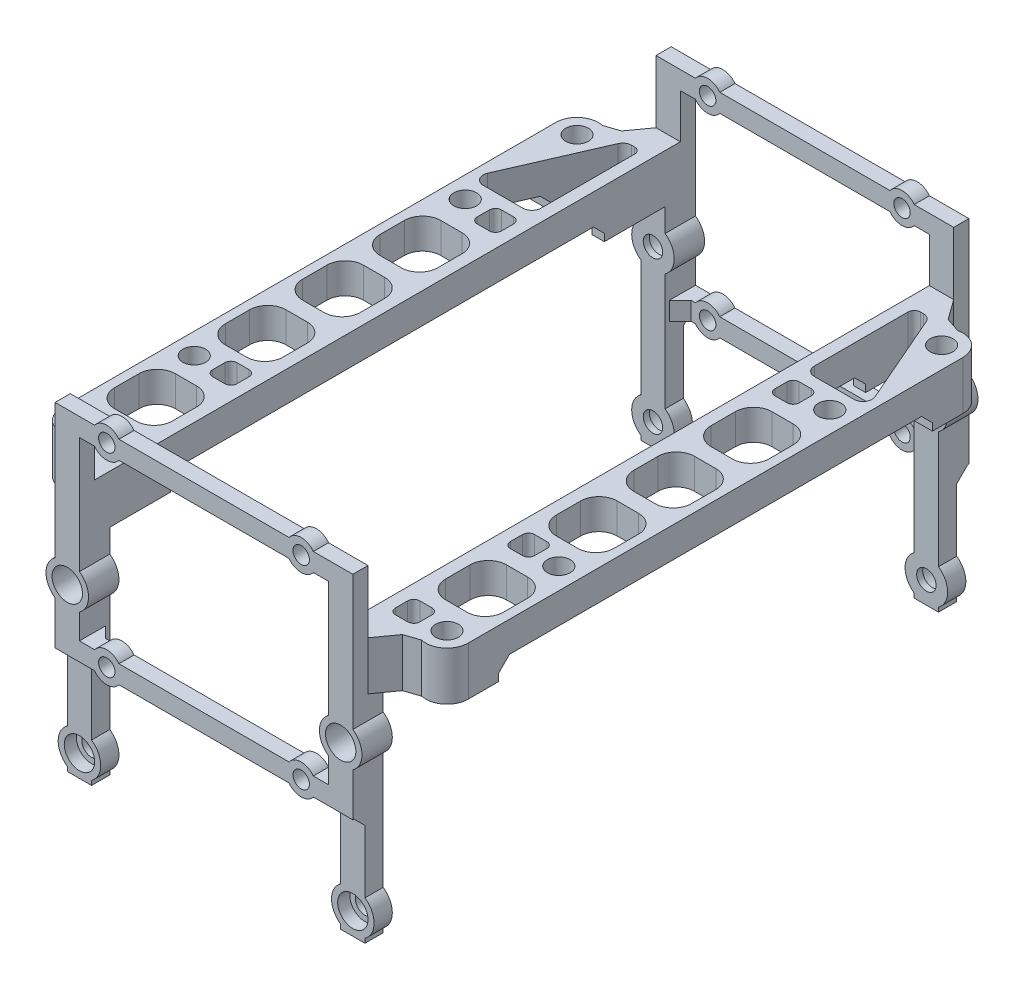
SolidWorks part; units mm, degrees
ref_plane "Front Plane" through (0, 0, 0) normal (0, 0, 1) x (1, 0, 0)
ref_plane "Top Plane" through (0, 0, 0) normal (0, 1, 0) x (1, 0, 0)
ref_plane "Right Plane" through (0, 0, 0) normal (1, 0, 0) x (0, 0, -1)
sketch "Sketch1" plane through (0, 0, 0) normal (1, 0, 0) x (0, 0, -1)
  line L0 (0, 0) -> (-3, 0)
  line L1 (0, 0) -> (91.4, 0) construction
  line L2 (0, 0) -> (0, 35.3)
  line L3 (0, 35.3) -> (91.4, 35.3) construction
  line L4 (91.4, 0) -> (91.4, 35.3)
  line L5 (-3, 0) -> (-3, 43.3)
  line L6 (-3, 43.3) -> (94.4, 43.3) construction
  line L7 (94.4, 43.3) -> (94.4, 0)
  line L8 (94.4, 0) -> (91.4, 0)
  line L9 (45.7, 43.3) -> (45.7, 35.3)
  line L10 (94.4, 43.3) -> (45.7, 43.3)
  line L11 (91.4, 35.3) -> (45.7, 35.3)
  dimension "D1" = 91.4
  dimension "D2" = 35.3
  dimension "D3" = 3
  dimension "D4" = 8
extrude "Boss-Extrude1" add sketch "Sketch1" along normal blind 4 contours L11 L4 L8 L7 L10 L9
sketch "Sketch2" plane through (0, 0, -94.4) normal (0, 0, 1) x (1, 0, 0)
  line L0 (2, 43.3) -> (2, 0) construction
  line L4 (4, 43.3) -> (0, 43.3) construction
  line L5 (4, 35.3) -> (0, 35.3) construction
  line L6 (4, 35.3) -> (0, 35.3) construction
  line L7 (4, 0) -> (0, 0) construction
  circle A0 centre (2, 28.6) radius 1.6
  circle A1 centre (2, 3.6) radius 1.6
  dimension "D1" = 3.2
  dimension "D2" = 25
  dimension "D3" = 6.7
extrude "Cut-Extrude1" cut sketch "Sketch2" along normal through all and the other way through all
sketch "Sketch3" plane through (0, 0, -94.4) normal (0, 0, -1) x (-1, 0, 0)
  line L0 (-2, 28.6) -> (43, 28.6) construction
  line L1 (20.5, 28.6) -> (0, 28.6) construction
  line L2 (6.5, 53.6) -> (20.5, 53.6)
  line L4 (0, 21.6) -> (2.5, 21.6)
  line L5 (20.5, 21.6) -> (20.5, 18.6)
  line L6 (20.5, 18.6) -> (6.5, 18.6)
  line L8 (-2, 3.6) -> (42.5, 3.6) construction
  line L9 (20.5, 20.1) -> (0, 20.1) construction
  line L11 (0, 53.6) -> (0, 50.6) construction
  line L12 (20.5, 50.6) -> (6.5, 50.6)
  line L13 (20.5, 53.6) -> (20.5, 50.6)
  line L14 (0, 53.6) -> (2.5, 53.6)
  line L15 (0, 52.1) -> (20.5, 52.1) construction
  line L16 (-4, 43.3) -> (-4, 53.6)
  line L17 (-4, 53.6) -> (0, 53.6)
  line L18 (-4, 43.3) -> (0, 43.3) construction
  line L19 (0, 43.3) -> (0, 50.6)
  line L20 (4.5, 52.1) -> (4.5, 20.1) construction
  line L21 (0, 21.6) -> (0, 18.6) construction
  line L22 (0, 43.3) -> (0, 0) construction
  line L23 (-4, 43.3) -> (0, 43.3) construction
  line L24 (-4, 43.3) -> (-4, 0) construction
  line L25 (2.5, 50.6) -> (0, 50.6)
  line L26 (6.5, 21.6) -> (20.5, 21.6)
  line L27 (2.5, 18.6) -> (0, 18.6)
  line L28 (-4, 43.3) -> (-4, 31.4723)
  line L29 (-4, 18.6) -> (0, 18.6)
  line L30 (0, 43.3) -> (0, 31.4723)
  line L31 (0, 25.7277) -> (0, 21.6)
  line L32 (-4, 25.7277) -> (-4, 18.6)
  circle A0 centre (4.5, 52.1) radius 1.35
  circle A1 centre (4.5, 20.1) radius 1.35
  arc A2 (2.5, 18.6) -> (6.5, 18.6) centre (4.5, 20.1) ccw
  arc A3 (6.5, 53.6) -> (2.5, 53.6) centre (4.5, 52.1) ccw
  circle A4 centre (-2, 28.6) radius 2.5
  arc A5 (2.5, 50.6) -> (6.5, 50.6) centre (4.5, 52.1) ccw
  arc A6 (6.5, 21.6) -> (2.5, 21.6) centre (4.5, 20.1) ccw
  circle A7 centre (-2, 28.6) radius 3.5
  circle M8 centre (-2, 28.6) radius 1.6
  line M31 (0, 43.3) -> (-4, 43.3)
  line M32 (0, 0) -> (0, 43.3)
  line M33 (-4, 43.3) -> (-4, 0)
  dimension "D5" = 2.7
  dimension "D7" = 5
  dimension "D8" = 5
  dimension "D9" = 7
  dimension "D1" = 45
  dimension "D2" = 3
  dimension "D3" = 15
  dimension "D4" = 32
  dimension "D6" = 16
extrude "Boss-Extrude2" add sketch "Sketch3" against normal blind 0.5 and the other way blind 2 contours L25 A5 L12 L13 L2 A3 L14 L17 L16 L19 A0 M31 | L26 A6 L4 L27 A2 L6 L5 A1 M32 | L29 M33 M32 M31 M8 | A7 M32 M31 M33 | A7 A4 M32 M33 | A7 A4 M32 | A7 A4 M33 | A7 A4 M33 M32
sketch "Sketch4" plane through (0, 0, -94.4) normal (0, 0, -1) x (-1, 0, 0)
  line L0 (20.5, 18.6) -> (20.5, 0) construction
  line L1 (-2, 3.6) -> (20.5, 3.6) construction
  circle A0 centre (-2, 3.6) radius 1.35
  circle A1 centre (-2, 3.6) radius 2.5
sketch "Sketch5" plane through (0, 43.3, 0) normal (0, 1, 0) x (1, 0, 0)
  line L0 (4, 45.7) -> (0, 45.7) construction
  line L1 (2, 45.7) -> (2, 91.4) construction
  line L3 (4, 91.4) -> (8.7463, 89.8179)
  line L4 (13, 86.4) -> (13, 45.7)
  line L5 (9.5, 91.4) -> (9.5, 45.6) construction
  line L8 (4, 91.4) -> (13, 88.4) construction
  line L9 (13, 88.4) -> (13, 45.7) construction
  line L10 (13, 45.7) -> (0, 45.7)
  line L11 (0, 45.7) -> (0, 91.4)
  line L12 (0, 91.4) -> (4, 91.4)
  line L13 (4, 93.9) -> (4, 45.7) construction
  line L14 (0, 93.9) -> (0, 45.7) construction
  line L15 (4, 93.9) -> (4, 45.7) construction
  line L16 (0.4, 91.4) -> (3.6, 91.4) construction
  circle A0 centre (9.5, 86.4) radius 1.875 construction
  arc A2 (13, 86.4) -> (8.7463, 89.8179) centre (9.5, 86.4) ccw
  circle A3 centre (4, 78.4) radius 3.5 construction
  circle A4 centre (4, 69.4) radius 3.5 construction
  circle A5 centre (4, 60.4) radius 3.5 construction
  dimension "D1" = 3.75
  dimension "D6" = 3.5
  dimension "D7" = 7
  dimension "D2" = 5
  dimension "D4" = 3.5
  dimension "D5" = 2
  dimension "D8" = 8
  dimension "D10" = 9
  dimension "D9" = 3
extrude "Boss-Extrude3" add sketch "Sketch5" against normal up to surface (8 mm away) up to face at (2, 35.3, -68.55)
sketch "Sketch9" plane through (0, 0, -94.4) normal (0, 0, -1) x (-1, 0, 0)
  circle A0 centre (4.5, 52.1) radius 1.35
  circle A1 centre (4.5, 52.1) radius 2.5
  circle A2 centre (4.5, 20.1) radius 1.35
  circle A3 centre (4.5, 20.1) radius 2.5
  circle A4 centre (-2, 28.6) radius 1.35
  circle A5 centre (-2, 28.6) radius 3.5
  circle A6 centre (-2, 3.6) radius 1.35 construction
  circle A7 centre (-2, 3.6) radius 1.35
  circle A8 centre (-2, 3.6) radius 2.7378
  arc A9 (6.5, 53.6) -> (2.5, 53.6) centre (4.5, 52.1) ccw construction
  circle A10 centre (4.5, 20.1) radius 2.5 construction
  dimension "D1" = 7
extrude "Boss-Extrude4" [suppressed] add sketch "Sketch9" along normal blind 2 contours A3 | A1 | A0 | A2
sketch "Sketch10" plane through (0, 0, -94.4) normal (0, 0, -1) x (-1, 0, 0)
  circle A0 centre (-2, 28.6) radius 1.6
  circle A1 centre (-2, 28.6) radius 3.5
  circle A2 centre (-2, 3.6) radius 1.6
  circle A3 centre (-2, 3.6) radius 3.5
  circle A4 centre (-2, 3.6) radius 1.6 construction
  circle A5 centre (-2, 28.6) radius 1.6 construction
  dimension "D1" = 7
extrude "Boss-Extrude5" add sketch "Sketch10" against normal up to surface (3 mm away) up to face at (3.6, 28.6, -91.4)
sketch "Sketch11" plane through (0, 0, -94.4) normal (0, 0, -1) x (-1, 0, 0)
  circle A0 centre (-2, 28.6) radius 2.5
  circle A1 centre (-2, 3.6) radius 2.5
  circle A3 centre (-2, 28.6) radius 1.6 construction
  dimension "D1" = 5
extrude "Cut-Extrude4" cut sketch "Sketch11" against normal blind 2
mirror "Mirror4" about plane through (-20.5, 0, -96.4) normal (-1, 0, 0) of bodies 115 108
mirror "Mirror5" about plane through (4, 0, -45.7) normal (0, 0, -1) of bodies 109
sketch "Sketch8" plane through (0, 43.3, 0) normal (0, 1, 0) x (1, 0, 0)
  line L0 (6.5, 34.4749) -> (6.5, 59.4749) construction
  line L1 (5, 50.2415) -> (8.5, 50.2415)
  line L2 (9.5, 86.4) -> (9.5, 5) construction
  line L3 (5, 62.9749) -> (8.5, 62.9749)
  line L6 (2, 88.4) -> (2, 72.9749)
  line L7 (3.5, 71.4749) -> (10, 71.4749)
  line L8 (11.3752, 73.5739) -> (4.8752, 88.4989)
  line L9 (3.5, 89.4) -> (3, 89.4)
  line L10 (0, 93.9) -> (0, -2.5) construction
  line L11 (2, 59.9749) -> (2, 55.9749)
  line L12 (13, 5) -> (13, 86.4) construction
  line L14 (5, 52.9749) -> (8.5, 52.9749)
  line L15 (11.5, 59.9749) -> (11.5, 55.9749)
  line L16 (3, 69.4749) -> (5, 69.4749)
  line L17 (2, 68.4749) -> (2, 66.4749)
  line L18 (3, 65.4749) -> (5, 65.4749)
  line L19 (6, 68.4749) -> (6, 66.4749)
  line L20 (2, 47.2415) -> (2, 43.2415)
  line L21 (5, 40.2415) -> (8.5, 40.2415)
  line L22 (11.5, 47.2415) -> (11.5, 43.2415)
  line L23 (6.5, 21.7415) -> (6.5, 46.7415) construction
  line L24 (5, 37.508) -> (8.5, 37.508)
  line L25 (2, 34.508) -> (2, 30.508)
  line L26 (5, 27.508) -> (8.5, 27.508)
  line L27 (11.5, 34.508) -> (11.5, 30.508)
  line L28 (6.5, 9.008) -> (6.5, 34.008) construction
  line L29 (9.5, 45.7) -> (-6.9785, 45.7) construction
  line L30 (6, 22.9251) -> (6, 24.9251)
  line L31 (3, 25.9251) -> (5, 25.9251)
  line L32 (2, 22.9251) -> (2, 24.9251)
  line L33 (3, 21.9251) -> (5, 21.9251)
  line L34 (9.5, 23.4) -> (-1.2891, 23.4) construction
  line L35 (11.5, 12.292) -> (11.5, 16.292)
  line L36 (5, 19.292) -> (8.5, 19.292)
  line L37 (2, 12.292) -> (2, 16.292)
  line L38 (5, 9.292) -> (8.5, 9.292)
  line L39 (-41, 91.4) -> (0, 91.4) construction
  line L40 (-20.5, 91.4) -> (-20.5, 40.2665) construction
  line L41 (-50.5, 23.4) -> (-39.7109, 23.4) construction
  line L42 (-50.5, 45.7) -> (-34.0215, 45.7) construction
  line L43 (-47.5, 9.008) -> (-47.5, 34.008) construction
  line L44 (-47.5, 21.7415) -> (-47.5, 46.7415) construction
  line L45 (-50.5, 86.4) -> (-50.5, 5) construction
  line L46 (-47.5, 34.4749) -> (-47.5, 59.4749) construction
  line L47 (-46, 9.292) -> (-49.5, 9.292)
  line L48 (-43, 12.292) -> (-43, 16.292)
  line L49 (-46, 19.292) -> (-49.5, 19.292)
  line L50 (-52.5, 12.292) -> (-52.5, 16.292)
  line L51 (-44, 21.9251) -> (-46, 21.9251)
  line L52 (-43, 22.9251) -> (-43, 24.9251)
  line L53 (-44, 25.9251) -> (-46, 25.9251)
  line L54 (-47, 22.9251) -> (-47, 24.9251)
  line L55 (-52.5, 34.508) -> (-52.5, 30.508)
  line L56 (-46, 27.508) -> (-49.5, 27.508)
  line L57 (-43, 34.508) -> (-43, 30.508)
  line L58 (-46, 37.508) -> (-49.5, 37.508)
  line L59 (-52.5, 47.2415) -> (-52.5, 43.2415)
  line L60 (-46, 40.2415) -> (-49.5, 40.2415)
  line L61 (-43, 47.2415) -> (-43, 43.2415)
  line L62 (-47, 68.4749) -> (-47, 66.4749)
  line L63 (-44, 65.4749) -> (-46, 65.4749)
  line L64 (-43, 68.4749) -> (-43, 66.4749)
  line L65 (-44, 69.4749) -> (-46, 69.4749)
  line L66 (-52.5, 59.9749) -> (-52.5, 55.9749)
  line L67 (-46, 52.9749) -> (-49.5, 52.9749)
  line L68 (-43, 59.9749) -> (-43, 55.9749)
  line L69 (-44.5, 89.4) -> (-44, 89.4)
  line L70 (-52.3752, 73.5739) -> (-45.8752, 88.4989)
  line L71 (-44.5, 71.4749) -> (-51, 71.4749)
  line L72 (-43, 88.4) -> (-43, 72.9749)
  line L73 (-46, 62.9749) -> (-49.5, 62.9749)
  line L74 (-46, 50.2415) -> (-49.5, 50.2415)
  line L75 (4, 91.4) -> (5.5, 91.4) construction
  line L76 (0, 93.9) -> (0, -2.5) construction
  line L77 (0, 93.9) -> (4, 93.9) construction
  line L78 (-41, 93.9) -> (-41, -2.5) construction
  line L79 (9.5, 23.4) -> (9.5, 5) construction
  line L80 (6, 3.9694) -> (6, 6.0306)
  line L81 (3, 7.0306) -> (5, 7.0306)
  line L82 (2, 4.0306) -> (2, 6.0306)
  line L83 (3, 3.0306) -> (5, 3.0306)
  line L84 (9.5, 5) -> (6, 5) construction
  line L85 (-44, 3.0306) -> (-46, 3.0306)
  line L86 (-43, 4.0306) -> (-43, 6.0306)
  line L87 (-44, 7.0306) -> (-46, 7.0306)
  line L88 (-47, 3.9694) -> (-47, 6.0306)
  arc A6 (10, 71.4749) -> (11.3752, 73.5739) centre (10, 72.9749) ccw
  arc A7 (2, 72.9749) -> (3.5, 71.4749) centre (3.5, 72.9749) ccw
  arc A8 (4.8752, 88.4989) -> (3.5, 89.4) centre (3.5, 87.9) ccw
  arc A9 (2, 88.4) -> (3, 89.4) centre (3, 88.4) cw
  arc A10 (13, 86.4) -> (8.7463, 89.8179) centre (9.5, 86.4) ccw construction
  arc A11 (13, 86.4) -> (8.7463, 89.8179) centre (9.5, 86.4) ccw construction
  circle A12 centre (9.5, 86.4) radius 1.875
  arc A13 (8.7463, 1.5821) -> (13, 5) centre (9.5, 5) ccw construction
  arc A14 (8.7463, 1.5821) -> (13, 5) centre (9.5, 5) ccw construction
  circle A15 centre (9.5, 5) radius 1.875
  circle A16 centre (9.5, 23.4) radius 1.875
  circle A17 centre (9.5, 68) radius 1.875
  arc A18 (5, 69.4749) -> (6, 68.4749) centre (5, 68.4749) cw
  arc A19 (6, 66.4749) -> (5, 65.4749) centre (5, 66.4749) cw
  arc A20 (3, 65.4749) -> (2, 66.4749) centre (3, 66.4749) cw
  arc A21 (2, 68.4749) -> (3, 69.4749) centre (3, 68.4749) cw
  arc A22 (8.5, 62.9749) -> (11.5, 59.9749) centre (8.5, 59.9749) cw
  arc A23 (11.5, 55.9749) -> (8.5, 52.9749) centre (8.5, 55.9749) cw
  arc A24 (5, 52.9749) -> (2, 55.9749) centre (5, 55.9749) cw
  arc A25 (2, 59.9749) -> (5, 62.9749) centre (5, 59.9749) cw
  arc A26 (8.5, 50.2415) -> (11.5, 47.2415) centre (8.5, 47.2415) cw
  arc A27 (2, 47.2415) -> (5, 50.2415) centre (5, 47.2415) cw
  arc A28 (5, 40.2415) -> (2, 43.2415) centre (5, 43.2415) cw
  arc A29 (11.5, 43.2415) -> (8.5, 40.2415) centre (8.5, 43.2415) cw
  arc A30 (8.5, 37.508) -> (11.5, 34.508) centre (8.5, 34.508) cw
  arc A31 (2, 34.508) -> (5, 37.508) centre (5, 34.508) cw
  arc A32 (5, 27.508) -> (2, 30.508) centre (5, 30.508) cw
  arc A33 (11.5, 30.508) -> (8.5, 27.508) centre (8.5, 30.508) cw
  arc A34 (2, 22.9251) -> (3, 21.9251) centre (3, 22.9251) ccw
  arc A35 (3, 25.9251) -> (2, 24.9251) centre (3, 24.9251) ccw
  arc A36 (6, 24.9251) -> (5, 25.9251) centre (5, 24.9251) ccw
  arc A37 (5, 21.9251) -> (6, 22.9251) centre (5, 22.9251) ccw
  arc A38 (11.5, 16.292) -> (8.5, 19.292) centre (8.5, 16.292) ccw
  arc A39 (5, 19.292) -> (2, 16.292) centre (5, 16.292) ccw
  arc A40 (2, 12.292) -> (5, 9.292) centre (5, 12.292) ccw
  arc A41 (8.5, 9.292) -> (11.5, 12.292) centre (8.5, 12.292) ccw
  arc A42 (-49.7463, 1.5821) -> (-54, 5) centre (-50.5, 5) cw construction
  arc A43 (-54, 86.4) -> (-49.7463, 89.8179) centre (-50.5, 86.4) cw construction
  arc A44 (-49.5, 9.292) -> (-52.5, 12.292) centre (-49.5, 12.292) cw
  arc A45 (-43, 12.292) -> (-46, 9.292) centre (-46, 12.292) cw
  arc A46 (-46, 19.292) -> (-43, 16.292) centre (-46, 16.292) cw
  arc A47 (-52.5, 16.292) -> (-49.5, 19.292) centre (-49.5, 16.292) cw
  arc A48 (-46, 21.9251) -> (-47, 22.9251) centre (-46, 22.9251) cw
  arc A49 (-47, 24.9251) -> (-46, 25.9251) centre (-46, 24.9251) cw
  arc A50 (-44, 25.9251) -> (-43, 24.9251) centre (-44, 24.9251) cw
  arc A51 (-43, 22.9251) -> (-44, 21.9251) centre (-44, 22.9251) cw
  arc A52 (-52.5, 30.508) -> (-49.5, 27.508) centre (-49.5, 30.508) ccw
  arc A53 (-46, 27.508) -> (-43, 30.508) centre (-46, 30.508) ccw
  arc A54 (-43, 34.508) -> (-46, 37.508) centre (-46, 34.508) ccw
  arc A55 (-49.5, 37.508) -> (-52.5, 34.508) centre (-49.5, 34.508) ccw
  arc A56 (-52.5, 43.2415) -> (-49.5, 40.2415) centre (-49.5, 43.2415) ccw
  arc A57 (-46, 40.2415) -> (-43, 43.2415) centre (-46, 43.2415) ccw
  arc A58 (-43, 47.2415) -> (-46, 50.2415) centre (-46, 47.2415) ccw
  arc A59 (-49.5, 50.2415) -> (-52.5, 47.2415) centre (-49.5, 47.2415) ccw
  arc A60 (-43, 59.9749) -> (-46, 62.9749) centre (-46, 59.9749) ccw
  arc A61 (-46, 52.9749) -> (-43, 55.9749) centre (-46, 55.9749) ccw
  arc A62 (-52.5, 55.9749) -> (-49.5, 52.9749) centre (-49.5, 55.9749) ccw
  arc A63 (-49.5, 62.9749) -> (-52.5, 59.9749) centre (-49.5, 59.9749) ccw
  arc A64 (-43, 68.4749) -> (-44, 69.4749) centre (-44, 68.4749) ccw
  arc A65 (-44, 65.4749) -> (-43, 66.4749) centre (-44, 66.4749) ccw
  arc A66 (-47, 66.4749) -> (-46, 65.4749) centre (-46, 66.4749) ccw
  arc A67 (-46, 69.4749) -> (-47, 68.4749) centre (-46, 68.4749) ccw
  circle A68 centre (-50.5, 68) radius 1.875
  circle A69 centre (-50.5, 23.4) radius 1.875
  circle A70 centre (-50.5, 5) radius 1.875
  circle A71 centre (-50.5, 86.4) radius 1.875
  arc A72 (-43, 88.4) -> (-44, 89.4) centre (-44, 88.4) ccw
  arc A73 (-45.8752, 88.4989) -> (-44.5, 89.4) centre (-44.5, 87.9) cw
  arc A74 (-43, 72.9749) -> (-44.5, 71.4749) centre (-44.5, 72.9749) cw
  arc A75 (-51, 71.4749) -> (-52.3752, 73.5739) centre (-51, 72.9749) cw
  arc A76 (2, 4.0306) -> (3, 3.0306) centre (3, 4.0306) ccw
  arc A77 (3, 7.0306) -> (2, 6.0306) centre (3, 6.0306) ccw
  arc A78 (6, 6.0306) -> (5, 7.0306) centre (5, 6.0306) ccw
  arc A79 (5, 3.0306) -> (6, 3.9694) centre (5.0019, 4.0306) ccw
  arc A80 (-46, 3.0306) -> (-47, 3.9694) centre (-46.0019, 4.0306) cw
  arc A81 (-47, 6.0306) -> (-46, 7.0306) centre (-46, 6.0306) cw
  arc A82 (-44, 7.0306) -> (-43, 6.0306) centre (-44, 6.0306) cw
  arc A83 (-43, 4.0306) -> (-44, 3.0306) centre (-44, 4.0306) cw
  dimension "D5" = 1.5
  dimension "D6" = 1
  dimension "D7" = 3.75
  dimension "D8" = 3.75
  dimension "D16" = 63
  dimension "D17" = 63
  dimension "D4" = 1
  dimension "D22" = 3
  dimension "D2" = 25
  dimension "D9" = 0.5
  dimension "D10" = 3
  dimension "D11" = 2
  dimension "D12" = 3.5
  dimension "D13" = 12
  dimension "D14" = 5.5
  dimension "D15" = 6.5
  dimension "D18" = 2
  dimension "D19" = 4
  dimension "D3" = 5
  dimension "D20" = 1.5
  dimension "D21" = 2.5
  dimension "D24" = 10
  dimension "D23" = 3
extrude "Cut-Extrude3" cut sketch "Sketch8" against normal through all
chamfer "Chamfer1" distance 2.5 8 edges at (4, 39.3, -91.4) (-45, 43.3, -92.65) (-45, 39.3, -91.4) (4, 43.3, 1.25) (4, 39.3, 0) (-45, 43.3, 1.25) (-45, 39.3, 0) (4, 43.3, -92.65)
sketch "Sketch12" plane through (0, 35.3, 0) normal (0, -1, 0) x (1, 0, 0)
  line L0 (0, 0) -> (-41, 0) construction
  line L1 (-20.5, 0) -> (-20.5, -83.4352) construction
  line L2 (0, -45.7) -> (-20.5, -45.7) construction
  line L3 (0, -91.4) -> (0, 0) construction
  circle A0 centre (9.5, -5) radius 3
  circle A1 centre (9.5, -23.4) radius 3
  circle A2 centre (9.5, -86.4) radius 3
  circle A3 centre (9.5, -68) radius 3
  circle A4 centre (-50.5, -86.4) radius 3
  circle A5 centre (-50.5, -68) radius 3
  circle A6 centre (-50.5, -23.4) radius 3
  circle A7 centre (-50.5, -5) radius 3
  dimension "D1" = 6
extrude "Cut-Extrude7" cut sketch "Sketch12" against normal blind 4.5
sketch "Sketch13" plane through (-54, 0, 0) normal (-1, 0, 0) x (0, 0, 1)
  line L0 (-45.7, 38.3) -> (-45.7, 43.3) construction
  line L1 (-81.4, 38.3) -> (-10, 38.3)
  line L2 (-81.4, 38.3) -> (-81.4, 30.9146)
  line L3 (-81.4, 30.9146) -> (-10, 30.9146)
  line L4 (-10, 38.3) -> (-10, 30.9146)
  line L5 (-5, 43.3) -> (-86.4, 43.3) construction
  line L6 (-5, 35.3) -> (-5, 43.3) construction
  line L7 (-5, 35.3) -> (-86.4, 35.3) construction
  dimension "D1" = 5
  dimension "D2" = 3
extrude "Cut-Extrude8" cut sketch "Sketch13" against normal through all
chamfer "Chamfer2" distance 1.8 angle 45 4 edges at (-43, 18.6, -94.4) (2, 18.6, 3) (-43, 18.6, 3) (2, 18.6, -94.4)
chamfer "Chamfer3" distance 1.8 angle 45 4 edges at (-41, 20.1, -93.9) (0, 20.1, -93.9) (0, 20.1, 2.5) (-41, 20.1, 2.5)
chamfer "Chamfer4" distance 1.8 angle 45 8 edges at (11.7178, 38.3, -10) (1.5322, 38.3, -10) (10.4834, 38.3, -81.4) (1, 38.3, -81.4) (-42.5322, 38.3, -10) (-52.7178, 38.3, -10) (-42, 38.3, -81.4) (-51.4834, 38.3, -81.4)
